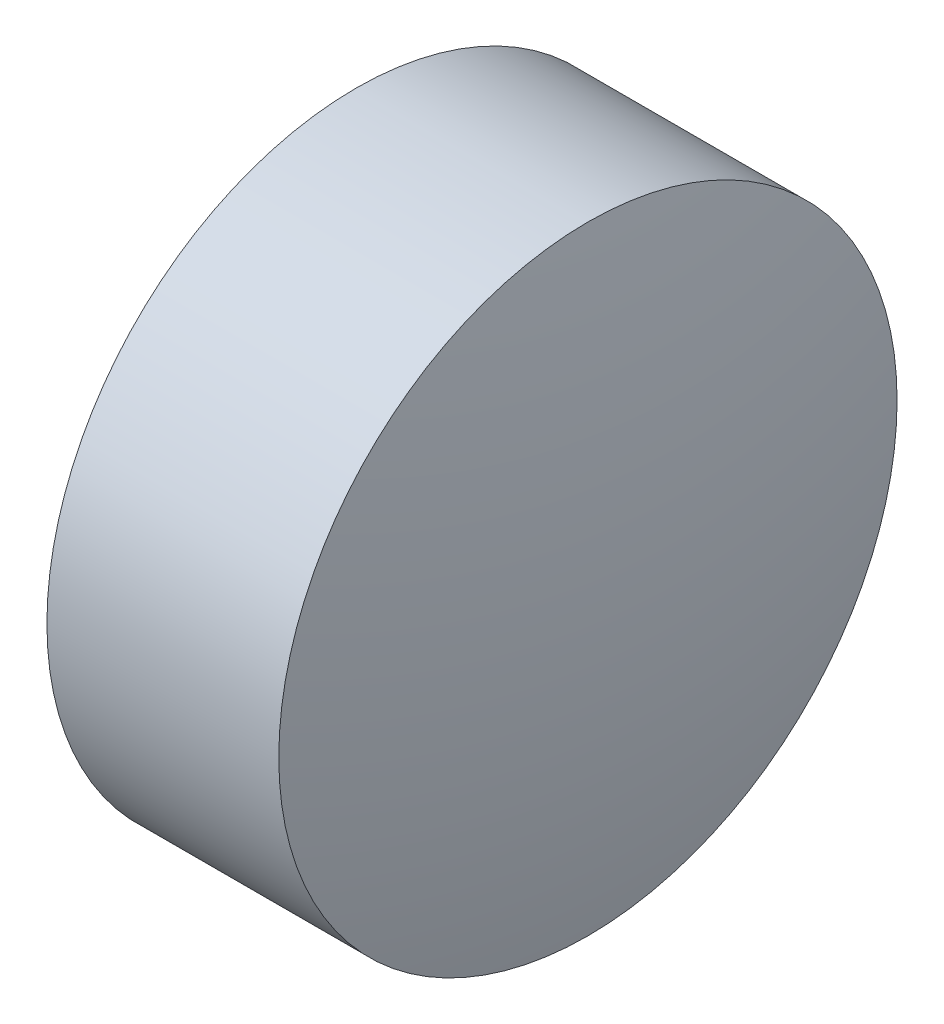
SolidWorks part; units mm, degrees
ref_plane "前视基准面" through (0, 0, 0) normal (0, 0, 1) x (1, 0, 0)
ref_plane "上视基准面" through (0, 0, 0) normal (0, 1, 0) x (1, 0, 0)
ref_plane "右视基准面" through (0, 0, 0) normal (1, 0, 0) x (0, 0, -1)
sketch "草图1" plane through (0, 0, 0) normal (0, 0, 1) x (1, 0, 0)
  line L0 (701.2058, 219.5476) -> (703.9033, 219.5476) construction
  line L1 (701.6339, 219.5476) -> (701.6339, 221.5476)
  line L2 (703.3539, 219.5476) -> (701.6339, 219.5476)
  line L5 (701.6339, 221.5476) -> (703.1339, 221.5476)
  arc A0 (703.3539, 219.5476) -> (703.1339, 221.5476) centre (694.153, 219.5476) ccw
revolve "旋转1" add sketch "草图1" angle 360 about L0
